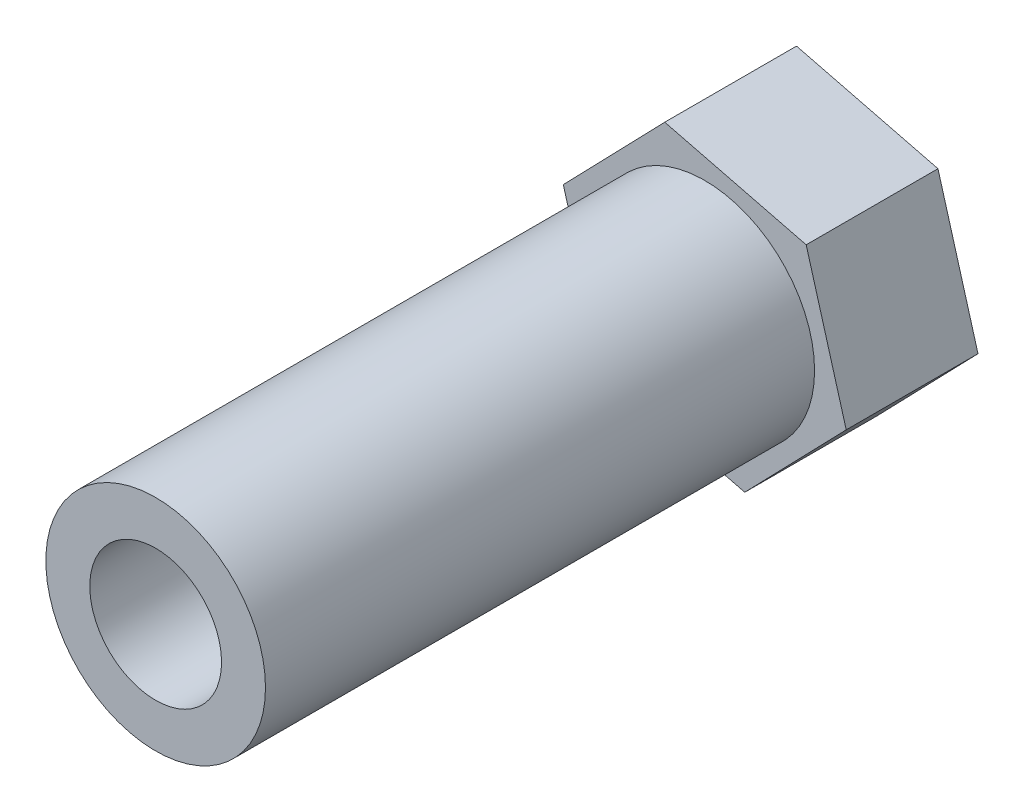
SolidWorks part; units mm, degrees
ref_plane "Plan de face" through (0, 0, 0) normal (0, 0, 1) x (1, 0, 0)
ref_plane "Plan de dessus" through (0, 0, 0) normal (0, 1, 0) x (1, 0, 0)
ref_plane "Plan de droite" through (0, 0, 0) normal (1, 0, 0) x (0, 0, -1)
sketch "Sketch1" plane through (0, 0, 0) normal (0, 0, 1) x (1, 0, 0)
  line L1 (-6.4405, 1.6136) -> (-4.6176, -4.7708)
  line L2 (-4.6176, -4.7708) -> (1.8228, -6.3844)
  line L3 (1.8228, -6.3844) -> (6.4405, -1.6136)
  line L4 (6.4405, -1.6136) -> (4.6176, 4.7708)
  line L5 (4.6176, 4.7708) -> (-1.8228, 6.3844)
  line L6 (-1.8228, 6.3844) -> (-6.4405, 1.6136)
  circle A0 centre (0, 0) radius 5.75 construction
  circle A1 centre (0, 0) radius 1.5
  dimension "D2" = 3
  dimension "D1" = 11.5
extrude "Boss-Extrude1" add sketch "Sketch1" along normal blind 6
sketch "Sketch2" plane through (0, 0, 6) normal (0, 0, 1) x (1, 0, 0)
  circle A0 centre (0, 0) radius 5
  circle A1 centre (0, 0) radius 3
  dimension "D1" = 10
  dimension "D2" = 6
extrude "Boss-Extrude2" add sketch "Sketch2" along normal blind 25
